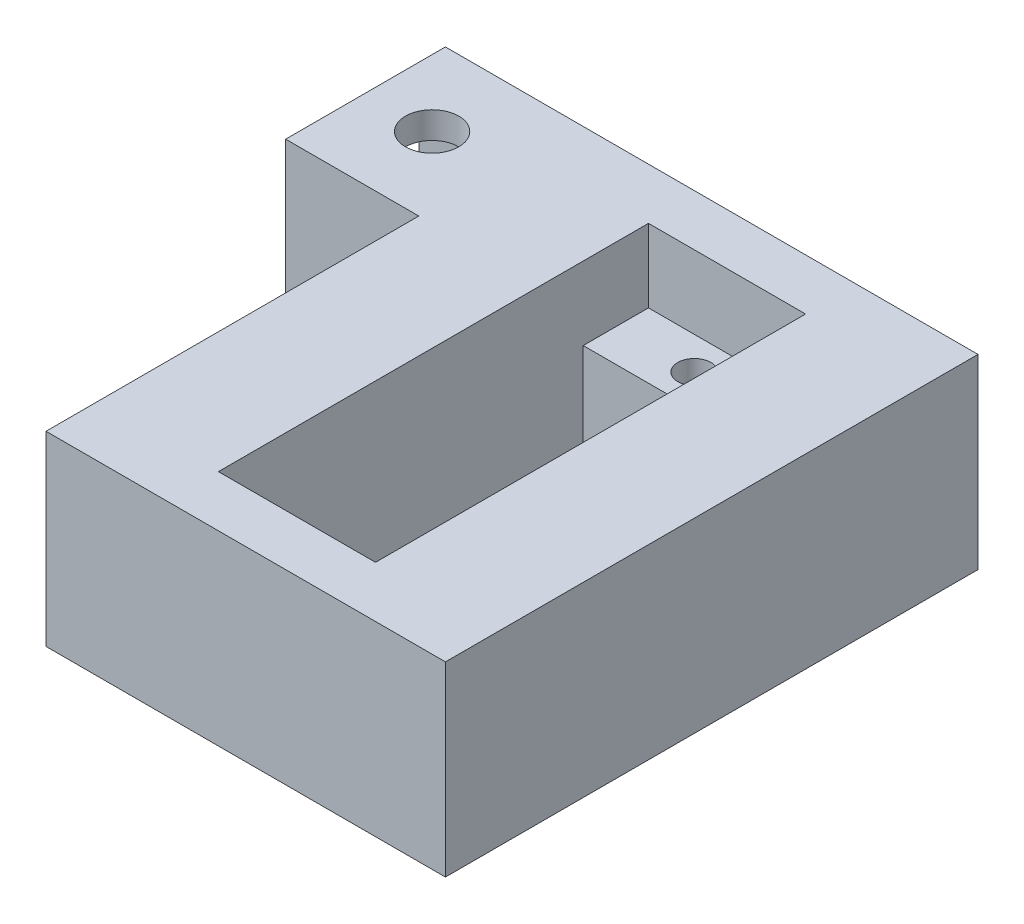
SolidWorks part; units mm, degrees
ref_plane "Front Plane" through (0, 0, 0) normal (0, 0, 1) x (1, 0, 0)
ref_plane "Top Plane" through (0, 0, 0) normal (0, 1, 0) x (1, 0, 0)
ref_plane "Right Plane" through (0, 0, 0) normal (1, 0, 0) x (0, 0, -1)
sketch "Sketch1" plane through (0, 0, 0) normal (0, 0, 1) x (1, 0, 0)
  line L1 (8.671, 9.0036) -> (-11.329, 9.0036)
  line L3 (11.4585, -4.9953) -> (8.671, -4.9953)
  line L5 (-11.329, -4.9953) -> (8.671, -4.9953)
  line L9 (8.671, 9.0036) -> (8.671, -4.9953)
  line L15 (-11.329, 9.0036) -> (-21.329, 9.0036)
  line L17 (-21.329, 9.0036) -> (-21.329, -4.9953)
  line L18 (-21.329, -4.9953) -> (-11.329, -4.9953)
  line L25 (18.8739, 13.2298) -> (8.671, 9.0036)
  line L26 (20.7873, 8.6104) -> (18.8739, 13.2298)
  line L27 (24.2314, 0.2955) -> (11.4585, -4.9953)
  line L28 (20.7873, 8.6104) -> (24.2314, 0.2955)
  dimension "D1" = 20
extrude "Boss-Extrude1" add sketch "Sketch1" along normal blind 40 contours L1 L15 L17 L18 L5 L9
sketch "Sketch3" plane through (0, 9.0036, 0) normal (0, 1, 0) x (1, 0, 0)
  line L0 (-6.329, -40) -> (-6.329, 0) construction
  line L1 (8.671, -40) -> (-21.329, -40) construction
  line L2 (-11.329, 0) -> (8.671, 0) construction
  line L3 (-21.329, -20) -> (8.671, -20) construction
  line L4 (-21.329, -40) -> (-21.329, 0) construction
  line L5 (8.671, -40) -> (8.671, 0) construction
  line L6 (-12.229, -31.25) -> (-0.429, -31.25)
  line L8 (-12.229, -3.85) -> (-12.229, -36.15)
  line L9 (-12.229, -36.15) -> (-0.429, -36.15)
  line L10 (-0.429, -3.85) -> (-0.429, -36.15)
  line L11 (-6.329, -31.25) -> (-6.329, -36.15) construction
  line L12 (-12.229, -3.85) -> (-0.429, -3.85)
  line L13 (-12.229, -8.75) -> (-0.429, -8.75)
  circle A0 centre (-6.329, -33.7) radius 1.25
  circle A1 centre (-6.329, -6.3) radius 1.25
  point P24 (-0.429, -20)
  point P26 (-12.229, -20)
  dimension "D1" = 11.8
  dimension "D2" = 5.9
  dimension "D3" = 16.15
  dimension "D4" = 4.9
sketch "Sketch4" plane through (0, 9.0036, 0) normal (0, 1, 0) x (1, 0, 0)
  line L0 (-12.229, -36.15) -> (-0.429, -36.15) construction
  line L1 (-0.429, -3.85) -> (-0.429, -36.15) construction
  line L2 (-12.229, -3.85) -> (-0.429, -3.85) construction
  line L3 (-12.229, -3.85) -> (-12.229, -36.15) construction
  line L4 (-12.229, -36.15) -> (-0.429, -36.15)
  line L5 (-0.429, -3.85) -> (-0.429, -36.15)
  line L6 (-12.229, -3.85) -> (-0.429, -3.85)
  line L7 (-12.229, -3.85) -> (-12.229, -36.15)
extrude "Cut-Extrude1" cut sketch "Sketch4" against normal blind 5.5
sketch "Sketch5" plane through (0, 3.5036, 0) normal (0, 1, 0) x (1, 0, 0)
  line L0 (-12.229, -31.25) -> (-0.429, -31.25) construction
  line L1 (-0.429, -3.85) -> (-0.429, -36.15) construction
  line L2 (-12.229, -3.85) -> (-12.229, -36.15) construction
  line L3 (-12.229, -8.75) -> (-0.429, -8.75) construction
  line L4 (-12.229, -31.25) -> (-0.429, -31.25)
  line L5 (-0.429, -8.75) -> (-0.429, -31.25)
  line L6 (-12.229, -8.75) -> (-12.229, -31.25)
  line L7 (-12.229, -8.75) -> (-0.429, -8.75)
extrude "Cut-Extrude2" cut sketch "Sketch5" against normal through all
sketch "Sketch6" plane through (0, 3.5036, 0) normal (0, 1, 0) x (1, 0, 0)
  circle A0 centre (-6.329, -6.3) radius 1.25
  circle A1 centre (-6.329, -33.7) radius 1.25
extrude "Cut-Extrude3" cut sketch "Sketch6" against normal through all
sketch "Sketch7" plane through (-21.329, 0, 0) normal (-1, 0, 0) x (0, 0, 1)
  line L0 (40, -4.9953) -> (0, -4.9953) construction
  line L1 (0, 9.0036) -> (12, 9.0036)
  line L2 (0, 9.0036) -> (0, -4.9953)
  line L3 (0, -4.9953) -> (12, -4.9953)
  line L4 (12, 9.0036) -> (12, -4.9953)
  dimension "D1" = 12
  dimension "D2" = 13.9988
extrude "Boss-Extrude2" add sketch "Sketch7" along normal blind 10
sketch "Sketch8" plane through (-31.329, 0, 0) normal (-1, 0, 0) x (0, 0, 1)
  line L0 (0, 9.0036) -> (0, -4.9953) construction
  line L1 (2, 7.0036) -> (10, 7.0036)
  line L2 (2, 7.0036) -> (2, -2.9953)
  line L3 (2, -2.9953) -> (10, -2.9953)
  line L4 (10, 7.0036) -> (10, -2.9953)
  line L5 (12, -4.9953) -> (12, 9.0036) construction
  line L6 (12, 9.0036) -> (0, 9.0036) construction
  line L7 (0, -4.9953) -> (12, -4.9953) construction
  dimension "D1" = 2
  dimension "D2" = 2
  dimension "D3" = 2
  dimension "D4" = 2
extrude "Cut-Extrude6" cut sketch "Sketch8" against normal blind 10
sketch "Sketch9" plane through (0, 9.0036, 0) normal (0, 1, 0) x (1, 0, 0)
  line L0 (-26.329, 0) -> (-26.329, -12) construction
  line L5 (-31.329, -6) -> (-21.329, -6) construction
  circle A0 centre (-26.329, -6) radius 2
extrude "Cut-Extrude7" cut sketch "Sketch9" against normal through all
